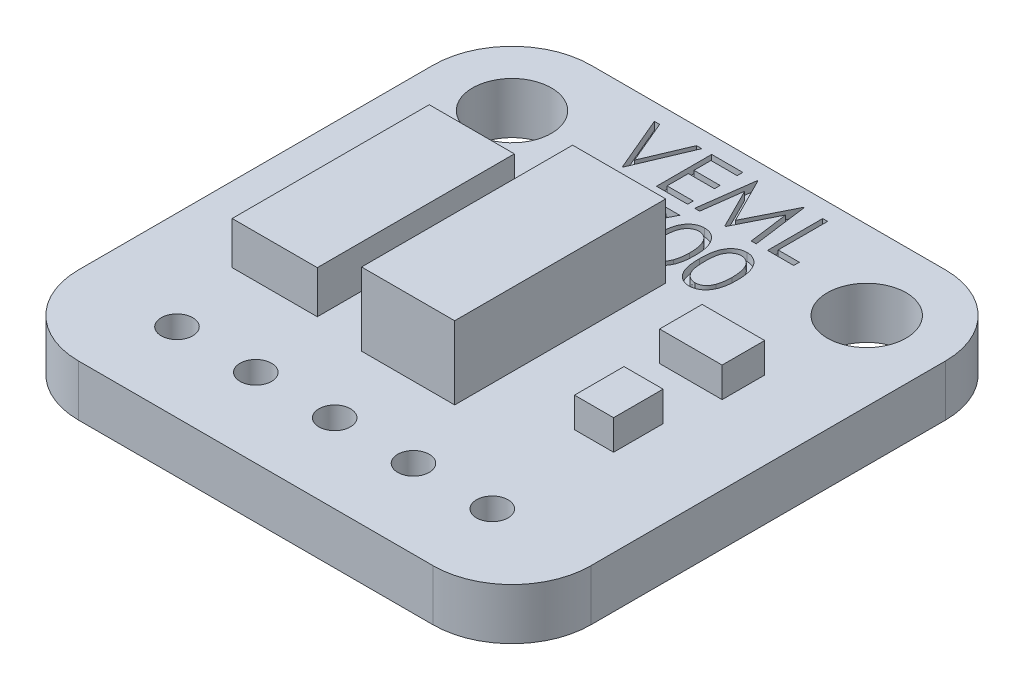
SolidWorks part; units mm, degrees
ref_plane "Front Plane" through (0, 0, 0) normal (0, 0, 1) x (1, 0, 0)
ref_plane "Top Plane" through (0, 0, 0) normal (0, 1, 0) x (1, 0, 0)
ref_plane "Right Plane" through (0, 0, 0) normal (1, 0, 0) x (0, 0, -1)
sketch "Sketch1" plane through (0, 0, 0) normal (0, 1, 0) x (1, 0, 0)
  line L1 (-8.255, -8.255) -> (8.255, -8.255)
  line L2 (-8.255, -8.255) -> (-8.255, 8.255)
  line L3 (-8.255, 8.255) -> (8.255, 8.255)
  line L4 (8.255, -8.255) -> (8.255, 8.255)
  line L5 (-8.255, -8.255) -> (8.255, 8.255) construction
  line L6 (-8.255, 8.255) -> (8.255, -8.255) construction
  point P0 (0, 0)
  dimension "D1" = 16.51
  dimension "D2" = 16.51
extrude "Boss-Extrude1" add sketch "Sketch1" along normal blind 1.651
sketch "Sketch2" plane through (0, 1.651, 0) normal (0, 1, 0) x (1, 0, 0)
  line L0 (0, 0) -> (0, 8.255) construction
  line L1 (8.255, 8.255) -> (-8.255, 8.255) construction
  circle A0 centre (-5.715, 5.715) radius 1.27
  circle A1 centre (5.715, 5.715) radius 1.27
  dimension "D1" = 2.54
  dimension "D2" = 11.43
  dimension "D3" = 2.54
extrude "Cut-Extrude1" cut sketch "Sketch2" against normal through all
fillet "Fillet1" radius 2.54 4 edges at (-8.255, 0.8255, -8.255) (8.255, 0.8255, -8.255) (8.255, 0.8255, 8.255) (-8.255, 0.8255, 8.255)
sketch "Sketch3" plane through (0, 1.651, 0) normal (0, 1, 0) x (1, 0, 0)
  line L0 (5.715, 8.255) -> (-5.715, 8.255) construction
  line L1 (-1.4252, 3.3782) -> (1.5748, 3.3782)
  line L2 (-1.4252, 3.3782) -> (-1.4252, -3.4218)
  line L3 (-1.4252, -3.4218) -> (1.5748, -3.4218)
  line L4 (1.5748, 3.3782) -> (1.5748, -3.4218)
  line L5 (8.255, -5.715) -> (8.255, 5.715) construction
  dimension "D1" = 3
  dimension "D2" = 6.8
  dimension "D3" = 4.8768
  dimension "D4" = 6.6802
extrude "Boss-Extrude2" add sketch "Sketch3" along normal blind 2.35 separate body
sketch "Sketch4" plane through (0, 1.651, 0) normal (0, 1, 0) x (1, 0, 0)
  line L0 (0, -8.255) -> (0, -5.715) construction
  line L1 (-5.715, -8.255) -> (5.715, -8.255) construction
  circle A0 centre (0, -5.715) radius 0.508
  dimension "D1" = 1.016
  dimension "D2" = 2.54
extrude "Cut-Extrude2" cut sketch "Sketch4" against normal through all
pattern_linear "LPattern1" count 3 spacing 2.54 along (1, 0, 0) count 3 spacing 2.54 along (-1, 0, 0) of "Cut-Extrude2"
sketch "Sketch5" plane through (0, 1.651, 0) normal (0, 1, 0) x (1, 0, 0)
  line L0 (-3.7136, 5.9318) -> (3.7136, 5.9318) construction
  line L1 (-3.7136, 3.7203) -> (3.7136, 3.7203) construction
  line L2 (0, 0) -> (0, 5.9318) construction
  text T0 "VEML" font "Century Gothic" height 1.778
  text T1 "7700" font "Century Gothic" height 1.778
  point P8 (0, 3.7203)
  point P9 (0.1217, 0)
  dimension "D1" = 7.4273
extrude "Cut-Extrude3" cut sketch "Sketch5" against normal blind 0.254
sketch "Sketch6" plane through (0, 1.651, 0) normal (0, 1, 0) x (1, 0, 0)
  line L0 (-3.0988, 0) -> (0, 0) construction
  line L1 (-5.842, 3.175) -> (-3.0988, 3.175)
  line L2 (-5.842, 3.175) -> (-5.842, -3.175)
  line L3 (-5.842, -3.175) -> (-3.0988, -3.175)
  line L4 (-3.0988, 3.175) -> (-3.0988, -3.175)
  line L5 (3.7211, 2.4061) -> (5.7356, 2.4061)
  line L6 (3.7211, 2.4061) -> (3.7211, 1.0352)
  line L7 (3.7211, 1.0352) -> (5.7356, 1.0352)
  line L8 (5.7356, 2.4061) -> (5.7356, 1.0352)
  line L9 (4.1968, -0.5875) -> (5.4558, -0.5875)
  line L10 (4.1968, -0.5875) -> (4.1968, -2.1823)
  line L11 (4.1968, -2.1823) -> (5.4558, -2.1823)
  line L12 (5.4558, -0.5875) -> (5.4558, -2.1823)
  line L13 (-8.255, 5.715) -> (-8.255, -5.715) construction
  dimension "D1" = 6.35
  dimension "D2" = 2.7432
  dimension "D3" = 2.413
extrude "Boss-Extrude3" add sketch "Sketch6" along normal offset from surface (1.3716 mm away) 3.0226 separate body up to face at (5.08, 0, 6.223)
sketch "Sketch7" plane through (0, 3.0226, 0) normal (0, 1, 0) x (1, 0, 0)
  line L1 (3.1336, 2.7978) -> (6.491, 2.7978)
  line L2 (3.1336, 2.7978) -> (3.1336, -2.63)
  line L3 (3.1336, -2.63) -> (6.491, -2.63)
  line L4 (6.491, 2.7978) -> (6.491, -2.63)
extrude "Cut-Extrude4" cut sketch "Sketch7" against normal offset from surface (0.4064 mm away) 2.6162 up to face at (5.08, 0, 6.223)
sketch "Sketch8" plane through (0, 1.651, 0) normal (0, 1, 0) x (1, 0, 0)
  line L1 (-1.2743, -2.8704) -> (1.2743, -2.8704)
  line L2 (-1.2743, -2.8704) -> (-1.2743, 2.8704)
  line L3 (-1.2743, 2.8704) -> (1.2743, 2.8704)
  line L4 (1.2743, -2.8704) -> (1.2743, 2.8704)
  line L5 (-1.2743, -2.8704) -> (1.2743, 2.8704) construction
  line L6 (-1.2743, 2.8704) -> (1.2743, -2.8704) construction
  point P0 (0, 0)
extrude "Boss-Extrude4" add sketch "Sketch8" along normal blind 0.762 separate body
sketch "Sketch9" plane through (0, 2.413, 0) normal (0, 1, 0) x (1, 0, 0)
  line L0 (0, 0) -> (0.6393, 0) construction
  line L1 (0.2583, -0.381) -> (1.0203, -0.381)
  line L2 (0.2583, -0.381) -> (0.2583, 0.381)
  line L3 (0.2583, 0.381) -> (1.0203, 0.381)
  line L4 (1.0203, -0.381) -> (1.0203, 0.381)
  line L5 (0.2583, -0.381) -> (1.0203, 0.381) construction
  line L6 (0.2583, 0.381) -> (1.0203, -0.381) construction
  line L7 (1.2743, -2.8704) -> (1.2743, 2.8704) construction
  point P0 (0.6393, 0)
  dimension "D1" = 0.762
  dimension "D2" = 0.254
extrude "Boss-Extrude5" add sketch "Sketch9" along normal blind 0.508 separate body
